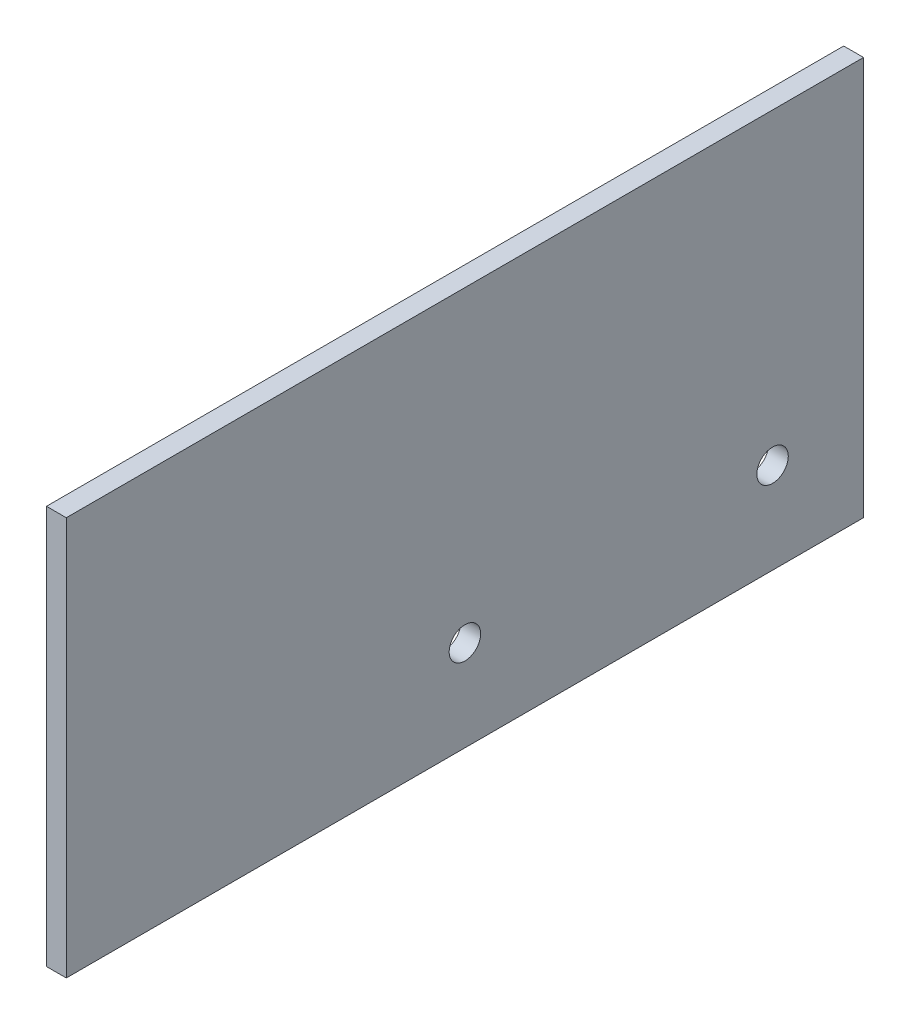
SolidWorks part; units mm, degrees
material "Black Acrylic"
ref_plane "Front Plane" through (0, 0, 0) normal (0, 0, 1) x (1, 0, 0)
ref_plane "Top Plane" through (0, 0, 0) normal (0, 1, 0) x (1, 0, 0)
ref_plane "Right Plane" through (0, 0, 0) normal (1, 0, 0) x (0, 0, -1)
sketch "Sketch1" plane through (0, 0, 0) normal (1, 0, 0) x (0, 0, -1)
  line L0 (-90.5, 0) -> (-90.5, -90.5)
  line L1 (-90.5, -90.5) -> (90.5, -90.5)
  line L2 (90.5, -90.5) -> (90.5, 0)
  line L3 (90.5, 0) -> (-90.5, 0)
  line L4 (90.5, -90.5) -> (-90.5, 90.5) construction
  line L5 (-90.5, -90.5) -> (90.5, 90.5) construction
  line L6 (90.5, -90.5) -> (90.5, 90.5) construction
  point P4 (0, 0)
  dimension "D1" = 181
  dimension "D2" = 181
extrude "Boss-Extrude1" add sketch "Sketch1" along normal mid plane 4.5
extrude "Cut-Extrude1" cut sketch "Sketch2" against normal through all both and the other way through all
sketch "Sketch2" plane through (88.25, 0, 0) normal (1, 0, 0) x (0, 0, -1)
  line L0 (0, -69.85) -> (0, 69.85) construction
  line L1 (0, 69.85) -> (-69.85, 69.85) construction
  line L2 (69.85, -69.85) -> (0, -69.85) construction
  circle A0 centre (0, -69.85) radius 3.5687
  circle A1 centre (-69.85, 69.85) radius 3.5687
  circle A2 centre (69.85, -69.85) radius 3.5687
  circle A3 centre (0, 69.85) radius 3.5687
